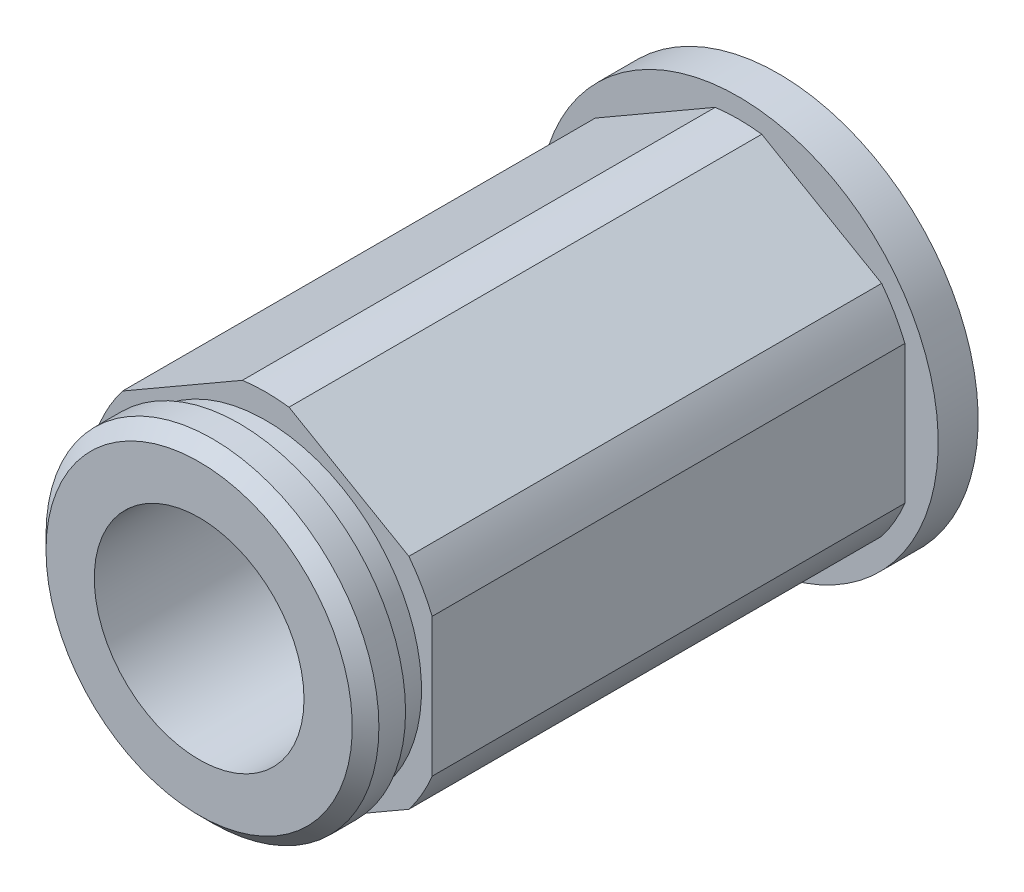
SolidWorks part; units mm, degrees
material "ThunderHex"
ref_plane "Front Plane" through (0, 0, 0) normal (0, 0, 1) x (1, 0, 0)
ref_plane "Top Plane" through (0, 0, 0) normal (0, 1, 0) x (1, 0, 0)
ref_plane "Right Plane" through (0, 0, 0) normal (1, 0, 0) x (0, 0, -1)
ref_plane "End1" through (0, 0, 9.779) normal (0, 0, 1) x (1, 0, 0)
ref_plane "End2" through (0, 0, -9.779) normal (0, 0, 1) x (1, 0, 0)
sketch "Sketch1" plane through (0, 0, 0) normal (0, 0, 1) x (1, 0, 0)
  circle A0 centre (0, 0) radius 6.35
  dimension "D1" = 12.7
extrude "Basic Rod" add sketch "Sketch1" along normal up to surface (9.779 mm away) and the other way up to surface (9.779 mm away) up to plane "End1" other way up to plane "End2"
ref_axis "Center Axis" through (0, 0, -38.2778) along (0, 0, 1)
sketch "Sketch8" plane through (0, 0, 0) normal (0, 0, 1) x (1, 0, 0)
  line L0 (-5.4616, 4.1791) -> (-6.35, 3.6662) construction
  line L1 (-0.8884, 6.8194) -> (-5.4616, 4.1791)
  line L2 (-6.35, 2.6403) -> (-6.35, -2.6403)
  line L3 (-5.4616, -4.1791) -> (-0.8884, -6.8194)
  line L4 (0.8884, -6.8194) -> (5.4616, -4.1791)
  line L5 (6.35, -2.6403) -> (6.35, 2.6403)
  line L6 (5.4616, 4.1791) -> (0.8884, 6.8194)
  line L7 (-6.35, 3.6662) -> (-6.35, 2.6403) construction
  line L8 (0, 7.3323) -> (-0.8884, 6.8194) construction
  line L9 (0.8884, 6.8194) -> (0, 7.3323) construction
  line L10 (6.35, 3.6662) -> (5.4616, 4.1791) construction
  line L11 (6.35, 2.6403) -> (6.35, 3.6662) construction
  line L12 (6.35, -3.6662) -> (6.35, -2.6403) construction
  line L13 (5.4616, -4.1791) -> (6.35, -3.6662) construction
  line L14 (0, -7.3323) -> (0.8884, -6.8194) construction
  line L15 (-0.8884, -6.8194) -> (0, -7.3323) construction
  line L16 (-6.35, -3.6662) -> (-5.4616, -4.1791) construction
  line L17 (-6.35, -2.6403) -> (-6.35, -3.6662) construction
  circle A0 centre (0, 0) radius 6.35 construction
  arc A1 (-6.35, -2.6403) -> (-5.4616, -4.1791) centre (0, 0) ccw
  circle A2 centre (0, 0) radius 6.35 construction
  arc A3 (-6.35, 2.6403) -> (-6.35, -2.6403) centre (0, 0) ccw construction
  arc A4 (-0.8884, 6.8194) -> (-5.4616, 4.1791) centre (0, 0) ccw construction
  arc A5 (-5.4616, 4.1791) -> (-6.35, 2.6403) centre (0, 0) ccw
  arc A6 (5.4616, 4.1791) -> (0.8884, 6.8194) centre (0, 0) ccw construction
  arc A7 (0.8884, 6.8194) -> (-0.8884, 6.8194) centre (0, 0) ccw
  arc A8 (6.35, -2.6403) -> (6.35, 2.6403) centre (0, 0) ccw construction
  arc A9 (6.35, 2.6403) -> (5.4616, 4.1791) centre (0, 0) ccw
  arc A10 (0.8884, -6.8194) -> (5.4616, -4.1791) centre (0, 0) ccw construction
  arc A11 (5.4616, -4.1791) -> (6.35, -2.6403) centre (0, 0) ccw
  arc A12 (-5.4616, -4.1791) -> (-0.8884, -6.8194) centre (0, 0) ccw construction
  arc A13 (-0.8884, -6.8194) -> (0.8884, -6.8194) centre (0, 0) ccw
  dimension "D1" = 13.7541
extrude "THex" add sketch "Sketch8" along normal mid plane 19.558
sketch "Sketch5" plane through (0, 0, 0) normal (0, 0, 1) x (1, 0, 0)
  line L1 (-3.6662, 6.35) -> (-7.3323, 0)
  line L2 (-7.3323, 0) -> (-3.6662, -6.35)
  line L3 (-3.6662, -6.35) -> (3.6662, -6.35)
  line L4 (3.6662, -6.35) -> (7.3323, 0)
  line L5 (7.3323, 0) -> (3.6662, 6.35)
  line L6 (3.6662, 6.35) -> (-3.6662, 6.35)
  circle A0 centre (0, 0) radius 6.35 construction
  circle A2 centre (0, 0) radius 6.35 construction
extrude "Hex" [suppressed] add sketch "Sketch5" along normal mid plane 19.558
sketch "Sketch7" plane through (0, 0, 0) normal (1, 0, 0) x (0, 0, -1)
  line L0 (0, 0) -> (-50000, 0) construction
  line L1 (-9.779, 5.9436) -> (-10.795, 5.9436)
  line L2 (-10.795, 5.9436) -> (-10.795, 6.35)
  line L3 (-10.795, 6.35) -> (-11.811, 6.35)
  line L4 (-12.319, 5.842) -> (-12.319, 0)
  line L5 (-12.319, 0) -> (-9.779, 0)
  line L6 (-9.779, 0) -> (-9.779, 5.9436)
  line L7 (-11.811, 6.35) -> (-12.319, 5.842)
  line L8 (38.2778, 0) -> (-38.2778, 0) construction
  line L9 (-9.779, 5.2388) -> (-9.779, -5.2388) construction
  point P7 (-12.319, 6.35)
  dimension "D1" = 12.7
  dimension "D4" = 1.016
  dimension "D2" = 0.4064
  dimension "D3" = 2.54
revolve "1stSnapRing" add sketch "Sketch7" angle 360 about axis through (0, 0, -38.2778) along (0, 0, 1)
mirror "2ndSnapRing" [suppressed] about plane through (0, 0, 0) normal (0, 0, 1)
sketch "Sketch2" plane through (0, 0, 0) normal (0, 0, 1) x (1, 0, 0)
  circle A0 centre (0, 0) radius 4.0005
  dimension "D1" = 8.001
extrude "Internal Cut" cut sketch "Sketch2" against normal through all both and the other way through all
sketch "Sketch9" plane through (0, 0, -9.779) normal (0, 0, -1) x (-1, 0, 0)
  circle A0 centre (0, 0) radius 7.62
  circle A1 centre (0, 0) radius 4.0005 construction
  circle A2 centre (0, 0) radius 4.0005
  dimension "D1" = 15.24
extrude "Boss-Extrude1" add sketch "Sketch9" against normal blind 1.524
equation "\"Unit Measure\"= \"Length\"'in"
equation "\"D1@Sketch1\"=\"OD\""
equation "\"D1\"= \"Length\""
equation "\"D1@Sketch2\"=\"ID\""
equation "\"Internal Cut\"= IIF ( \"ID\" = 0 ,  suppressed  ,  unsuppressed  ) "
equation "\"D1@Hex\" = \"Length\""
equation "\"Hex\" = IIF ( \"SelectionType\" = 1 , \"suppressed\" , iif ( \"SelectionType\" = 2 , \"suppressed\" , \"unsuppressed\" ) )"
equation "\"OutsideDiameter\"= \"OD\"'in"
equation "\"ThunderHexDia\"= iif ( \"OD\" < .36 , \"OD\" * 1.1 , iif ( \"OD\" < .40 , .4035 , iif ( \"OD\" < .52 , .5415 , \"OD\" * 1.1 ) ) )"
equation "\"D1@Sketch7\"=\"Thickness\""
equation "\"SRDia\"= iif ( \"OD\" = .5 , ( \"OD\" - .468 ) / 2 , iif ( \"OD\" = .375 , ( \"OD\" - .352 ) / 2 , .050 ) )"
equation "\"D2@Sketch7\"= \"SnapRingDepth\""
equation "\"1stSnapRing\"= iif ( \"SnapRingCount\" > 0 , \"unsuppressed\" , \"suppressed\" )"
equation "\"2ndSnapRing\"= iif ( \"SnapRingCount\" = 2 , \"unsuppressed\" , \"suppressed\" )"
equation "\"D1@End1\" = \"Length\" / 2"
equation "\"D1@End2\" = \"Length\""
equation "\"D1@Sketch8\"=\"ThunderHexDia\""
equation "\"D1@THex\" = \"Length\""
equation "\"THex\"= IIF ( \"SelectionType\" = 0 ,  suppressed  , iif ( \"SelectionType\" = 2 ,  suppressed  ,  unsuppressed  )  ) "
